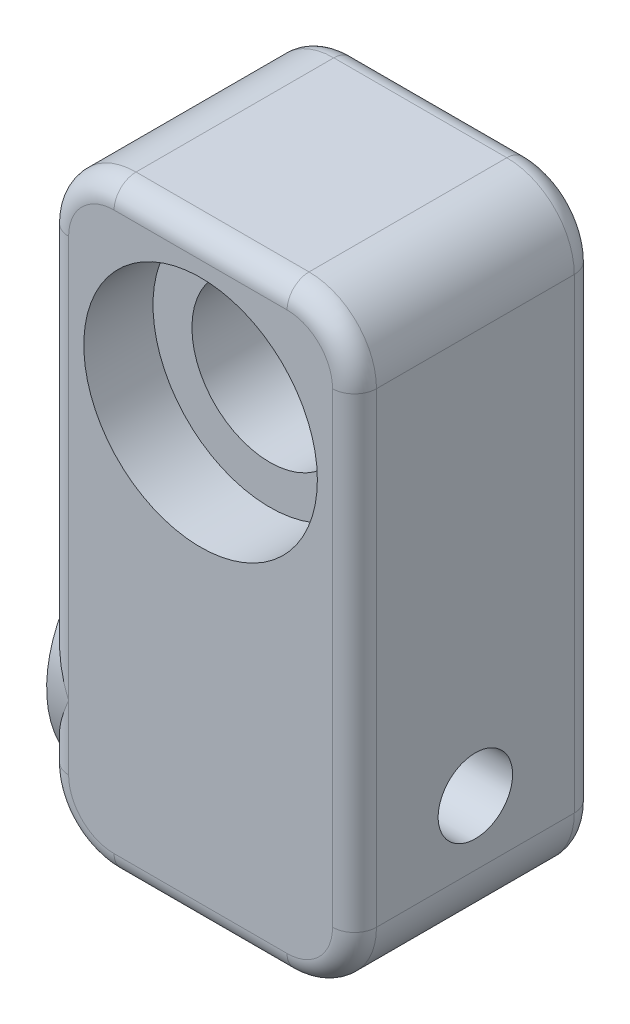
SolidWorks part; units mm, degrees
ref_plane "Front Plane" through (0, 0, 0) normal (0, 0, 1) x (1, 0, 0)
ref_plane "Top Plane" through (0, 0, 0) normal (0, 1, 0) x (1, 0, 0)
ref_plane "Right Plane" through (0, 0, 0) normal (1, 0, 0) x (0, 0, -1)
sketch "Sketch1" plane through (0, 0, 0) normal (0, 0, 1) x (1, 0, 0)
  line L0 (5, -6.127) -> (-5, -6.127) construction
  line L1 (6.127, 5) -> (6.127, -5) construction
  line L2 (-5, 6.127) -> (5, 6.127) construction
  line L3 (-6.127, -5) -> (-6.127, 5) construction
  line L4 (5, -6.127) -> (-5, -6.127) construction
  line L5 (6.127, 5) -> (6.127, -5) construction
  line L6 (-5, 6.127) -> (5, 6.127) construction
  line L7 (-6.127, -5) -> (-6.127, 5) construction
  line L8 (-6.127, -5) -> (-6.127, -21.956) construction
  line L9 (-5, -23.083) -> (5, -23.083) construction
  line L10 (6.127, -5) -> (6.127, -21.956) construction
  line L11 (-8.897, -5) -> (-8.897, -21.956)
  line L12 (-5, -25.853) -> (5, -25.853)
  line L13 (8.897, -5) -> (8.897, -21.956)
  line L14 (8.897, 5) -> (8.897, -5)
  line L15 (-5, 8.897) -> (5, 8.897)
  line L16 (-8.897, -5) -> (-8.897, 5)
  line L18 (-6.5, 8.897) -> (6.5, 8.897) construction
  arc A0 (-6.127, -5) -> (-5, -6.127) centre (-5, -5) ccw construction
  arc A1 (5, -6.127) -> (6.127, -5) centre (5, -5) ccw construction
  arc A2 (6.127, 5) -> (5, 6.127) centre (5, 5) ccw construction
  arc A3 (-5, 6.127) -> (-6.127, 5) centre (-5, 5) ccw construction
  arc A4 (-6.127, -5) -> (-5, -6.127) centre (-5, -5) ccw construction
  arc A5 (5, -6.127) -> (6.127, -5) centre (5, -5) ccw construction
  arc A6 (6.127, 5) -> (5, 6.127) centre (5, 5) ccw construction
  arc A7 (-5, 6.127) -> (-6.127, 5) centre (-5, 5) ccw construction
  arc A8 (-6.127, -21.956) -> (-5, -23.083) centre (-5, -21.956) ccw construction
  arc A9 (6.127, -21.956) -> (5, -23.083) centre (5, -21.956) cw construction
  arc A10 (-8.897, -21.956) -> (-5, -25.853) centre (-5, -21.956) ccw
  arc A11 (8.897, -21.956) -> (5, -25.853) centre (5, -21.956) cw
  arc A12 (8.897, 5) -> (5, 8.897) centre (5, 5) ccw
  arc A13 (-5, 8.897) -> (-8.897, 5) centre (-5, 5) ccw
  dimension "D1" = 29.21
extrude "Boss-Extrude1" add sketch "Sketch1" along normal blind 13.97 contours L7 A7 L6 A6 L5 L10 A9 L9 A8 L8
fillet "Fillet1" radius 1.27 16 edges at (-7.7556, 7.7556, 13.97) (0, 8.897, 13.97) (7.7556, 7.7556, 13.97) (8.897, -8.478, 13.97) (7.7556, -24.7116, 13.97) (0, -25.853, 13.97) (-7.7556, -24.7116, 13.97) (-8.897, -8.478, 13.97) (7.7556, -24.7116, 0) (0, -25.853, 0) (-7.7556, -24.7116, 0) (-8.897, -8.478, 0) (-7.7556, 7.7556, 0) (0, 8.897, 0) (7.7556, 7.7556, 0) (8.897, -8.478, 0)
hole_wizard "CBORE for M8 SHCS1" positions "Sketch2" profile "Sketch3" counterbore size "M8" standard "ANSI Metric" end condition through all
sketch "Sketch2" plane through (0, 0, 13.97) normal (0, 0, 1) x (1, 0, 0)
  circle A0 centre (0, 0) radius 4 construction
  point P0 (0, 0)
sketch "Sketch3" plane through (0, 0, 13.97) normal (1, 0, 0) x (0, -1, 0)
  line L0 (0, 0) -> (0, 13.97)
  line L1 (0, 13.97) -> (4.5, 13.97)
  line L3 (4.5, 13.97) -> (4.5, 4)
  line L4 (4.5, 4) -> (6.75, 4)
  line L5 (6.75, 4) -> (6.75, 0)
  line L7 (6.75, 0) -> (0, 0)
  line L11 (0, -6.35) -> (0, 107.95) construction
  dimension "Thru Hole Dia." = 9
  dimension "Thru Hole Depth" = 13.97
  dimension "C'Bore Dia." = 13.5
  dimension "C'Bore Depth" = 4
hole_wizard "M4 Clearance Hole1" positions "Sketch4" profile "Sketch5" hole size "M4" standard "ANSI Metric" end condition through all
sketch "Sketch4" plane through (8.897, 0, 0) normal (1, 0, 0) x (0, 0, -1)
  line L5 (-12.7, -25.853) -> (-1.27, -25.853) construction
  line L6 (-13.97, -18.233) -> (0, -18.233) construction
  line L7 (-13.97, -21.956) -> (-13.97, 5) construction
  line L8 (0, -21.956) -> (0, 5) construction
  point P0 (-6.985, -18.233)
  dimension "D1" = 7.62
sketch "Sketch5" plane through (8.897, -18.233, 6.985) normal (0, 1, 0) x (0, 0, -1)
  line L0 (0, 0) -> (0, 17.794)
  line L1 (0, 17.794) -> (2.15, 17.794)
  line L2 (2.15, 17.794) -> (2.15, 0)
  line L5 (2.15, 0) -> (0, 0)
  line L11 (0, -6.35) -> (0, 107.95) construction
  dimension "Thru Hole Dia." = 4.3
  dimension "Thru Hole Depth" = 17.794
sketch "Sketch6" plane through (0, 0, 0) normal (0, 0, 1) x (1, 0, 0)
  line L0 (3.25, 5.6292) -> (0, 7.5056) construction
  line L1 (6.5, 3.7528) -> (3.25, 5.6292) construction
  line L2 (6.5, 0) -> (6.5, 3.7528) construction
  line L3 (6.5, -3.7528) -> (6.5, 0) construction
  line L4 (3.25, -5.6292) -> (6.5, -3.7528) construction
  line L5 (0, -7.5056) -> (3.25, -5.6292) construction
  line L6 (-3.25, -5.6292) -> (0, -7.5056) construction
  line L7 (-6.5, -3.7528) -> (-3.25, -5.6292) construction
  line L8 (-6.5, 0) -> (-6.5, -3.7528) construction
  line L9 (-6.5, 3.7528) -> (-6.5, 0) construction
  line L10 (-3.25, 5.6292) -> (-6.5, 3.7528) construction
  line L11 (0, 7.5056) -> (-3.25, 5.6292) construction
  line L12 (3.25, 5.6292) -> (0, 7.5056) construction
  line L13 (6.5, 3.7528) -> (3.25, 5.6292) construction
  line L14 (6.5, 0) -> (6.5, 3.7528) construction
  line L15 (6.5, -3.7528) -> (6.5, 0) construction
  line L16 (3.25, -5.6292) -> (6.5, -3.7528) construction
  line L17 (0, -7.5056) -> (3.25, -5.6292) construction
  line L18 (-3.25, -5.6292) -> (0, -7.5056) construction
  line L19 (-6.5, -3.7528) -> (-3.25, -5.6292) construction
  line L20 (-6.5, 0) -> (-6.5, -3.7528) construction
  line L21 (-6.5, 3.7528) -> (-6.5, 0) construction
  line L22 (-3.25, 5.6292) -> (-6.5, 3.7528) construction
  line L23 (0, 7.5056) -> (-3.25, 5.6292) construction
  line L24 (3.25, 5.6292) -> (0, 7.5056)
  line L25 (0, 7.5056) -> (-3.25, 5.6292)
  line L26 (-3.25, 5.6292) -> (-6.5, 3.7528)
  line L27 (-6.5, 3.7528) -> (-6.5, 0)
  line L28 (-6.5, 0) -> (-6.5, -3.7528)
  line L29 (-6.5, -3.7528) -> (-3.25, -5.6292)
  line L30 (-3.25, -5.6292) -> (0, -7.5056)
  line L31 (0, -7.5056) -> (3.25, -5.6292)
  line L32 (3.25, -5.6292) -> (6.5, -3.7528)
  line L33 (6.5, -3.7528) -> (6.5, 0)
  line L34 (6.5, 0) -> (6.5, 3.7528)
  line L35 (6.5, 3.7528) -> (3.25, 5.6292)
  line L37 (-7.5056, 0) -> (-3.7528, -6.5)
  line L38 (-3.7528, -6.5) -> (3.7528, -6.5)
  line L39 (3.7528, -6.5) -> (7.5056, 0)
  line L40 (7.5056, 0) -> (3.7528, 6.5)
  line L41 (3.7528, 6.5) -> (-3.7528, 6.5)
  line L42 (-3.7528, 6.5) -> (-7.5056, 0)
  circle A0 centre (0, 0) radius 6.5 construction
  line M23 (7.627, 5) -> (7.627, -21.956)
  line M27 (-7.627, -21.956) -> (-7.627, 5)
  line M29 (-5, 7.627) -> (5, 7.627)
  circle M31 centre (0, 0) radius 4.5
  dimension "D1" = 0
extrude "Cut-Extrude1" cut sketch "Sketch6" along normal blind 4 contours L42 L26 L25 L41 L24 L35 L40 L34 L33 L39 L32 L31 L38 L30 L29 L37 L28 L27 M31 | M31 | L34 L40 L35 | L40 L39 L33 L34 M23 | L40 L39 M23 | L32 L39 L33 | L39 L38 L31 L32 | L41 L40 L35 L24 | L24 L41 L25 M29 | L25 L24 M29 | L26 L42 L27 | L42 L27 L28 L37 M27 | L42 L37 M27 | L28 L37 L29 | L38 L37 L29 L30 | L30 L38 L31 | L42 L41 L25 L26
sketch "Sketch9" plane through (-8.897, 0, 0) normal (-1, 0, 0) x (0, 0, 1)
  line L0 (0, -21.956) -> (0, 5) construction
  circle A0 centre (6.985, -18.233) radius 2.15 construction
  circle A1 centre (6.985, -18.233) radius 2.15
  circle A2 centre (6.985, -18.233) radius 6.985
extrude "Boss-Extrude3" add sketch "Sketch9" against normal up to next
equation "\"D1@Boss-Extrude3\"=(1.438380in)/2"
